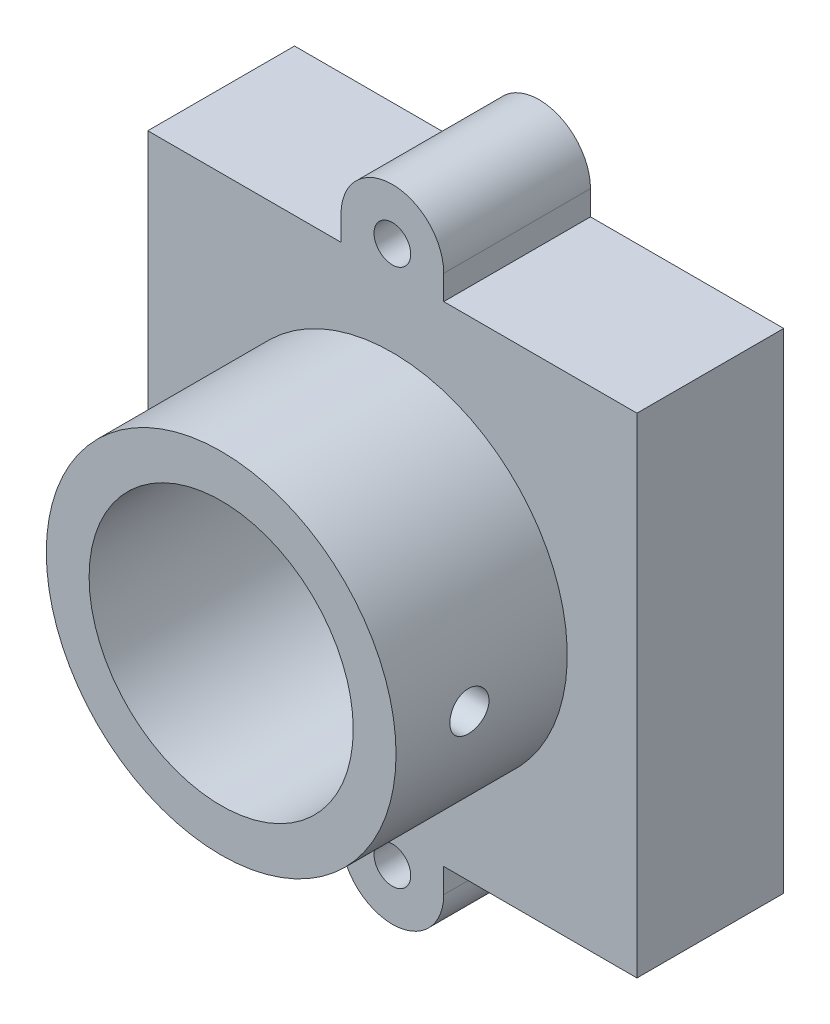
SolidWorks part; units mm, degrees
ref_plane "Ebene vorne" through (0, 0, 0) normal (0, 0, 1) x (1, 0, 0)
ref_plane "Ebene oben" through (0, 0, 0) normal (0, 1, 0) x (1, 0, 0)
ref_plane "Ebene rechts" through (0, 0, 0) normal (1, 0, 0) x (0, 0, -1)
ref_plane "Ebene1" through (0, 0, 0) normal (0, 0, -1) x (-1, 0, 0)
sketch "Skizze1" plane through (0, 0, 0) normal (0, 0, -1) x (-1, 0, 0)
  line L0 (2.1, -11) -> (2.1, 11)
  line L1 (-2.1, 11) -> (-2.1, -11)
  arc A0 (-2.1, -11) -> (2.1, -11) centre (0, -11) ccw
  arc A1 (2.1, 11) -> (-2.1, 11) centre (0, 11) ccw
extrude "Aufsatz-Linear austragen1" add sketch "Skizze1" against normal blind 6
sketch "Skizze2" plane through (-2.1, 0, 0) normal (-1, 0, 0) x (0, 0, 1)
  line L0 (6, -10) -> (0, -10)
  line L1 (0, -10) -> (0, 10)
  line L2 (0, 10) -> (6, 10)
  line L3 (6, 10) -> (6, -10)
extrude "Aufsatz-Linear austragen2" add sketch "Skizze2" along normal blind 7.9
sketch "Skizze3" plane through (2.1, 0, 0) normal (1, 0, 0) x (0, 0, -1)
  line L0 (-6, 10) -> (0, 10)
  line L1 (0, 10) -> (0, -10)
  line L2 (0, -10) -> (-6, -10)
  line L3 (-6, -10) -> (-6, 10)
extrude "Aufsatz-Linear austragen3" add sketch "Skizze3" along normal blind 7.9
sketch "Skizze4" plane through (0, 0, 6) normal (0, 0, 1) x (1, 0, 0)
  circle A0 centre (0, 0) radius 7.15
extrude "Aufsatz-Linear austragen4" add sketch "Skizze4" along normal blind 7
sketch "Skizze5" plane through (0, 0, 0) normal (0, 0, -1) x (-1, 0, 0)
  line L0 (-9.5, 9.5) -> (-9.5, -9.5)
  line L1 (-9.5, -9.5) -> (9.5, -9.5)
  line L2 (9.5, -9.5) -> (9.5, 9.5)
  line L3 (9.5, 9.5) -> (-9.5, 9.5)
extrude "Schnitt-Linear austragen1" cut sketch "Skizze5" against normal blind 1.3
sketch "Skizze6" plane through (0, 0, 1.3) normal (0, 0, -1) x (-1, 0, 0)
  line L0 (9, -9) -> (9, 9)
  line L1 (9, 9) -> (-9, 9)
  line L2 (-9, 9) -> (-9, -9)
  line L3 (-9, -9) -> (9, -9)
extrude "Schnitt-Linear austragen2" cut sketch "Skizze6" against normal blind 3.7
hole_wizard "Ø1.5 (1.5) Durchmesser Bohrung1" positions "Skizze8" profile "Skizze7" hole size "Ø1.5" standard "Ansi Metrisch"
sketch "Skizze8" plane through (0, 0, 0) normal (0, 0, -1) x (-1, 0, 0)
  point P0 (0, -11)
  point P1 (0, 11)
sketch "Skizze7" plane through (0, -11, 0) normal (1, 0, 0) x (0, 1, 0)
  line L0 (0, 0) -> (0, 13)
  line L1 (0, 13) -> (0.75, 13)
  line L2 (0.75, 13) -> (0.75, 0)
  line L5 (0.75, 0) -> (0, 0)
  line L11 (0, -6.35) -> (0, 107.95) construction
  dimension "Bohrerdurchmesser" = 1.5
  dimension "Bohrungstiefe" = 13
hole_wizard "Ø10.8 (10.8) Durchmesser Bohrung1" positions "Skizze10" profile "Skizze9" hole size "Ø10.8" standard "Ansi Metrisch"
sketch "Skizze10" plane through (0, 0, 13) normal (0, 0, 1) x (1, 0, 0)
  point P0 (0, 0)
sketch "Skizze9" plane through (0, 0, 13) normal (1, 0, 0) x (0, -1, 0)
  line L0 (0, 0) -> (0, 13)
  line L1 (0, 13) -> (5.4, 13)
  line L2 (5.4, 13) -> (5.4, 0)
  line L5 (5.4, 0) -> (0, 0)
  line L11 (0, -6.35) -> (0, 107.95) construction
  dimension "Bohrerdurchmesser" = 10.8
  dimension "Bohrungstiefe" = 13
hole_wizard "Ø1.6 (1.6) Durchmesser Bohrung1" positions "3D-Skizze1" profile "Skizze11" hole size "Ø1.6" standard "Ansi Metrisch"
sketch3d "3D-Skizze1"
  point P0 (7.15, 0, 10)
sketch "Skizze11" plane through (7.15, 0, 10) normal (0, 1, 0) x (0, 0, -1)
  line L0 (0, 0) -> (0, 1.75)
  line L1 (0, 1.75) -> (0.8, 1.75)
  line L2 (0.8, 1.75) -> (0.8, 0)
  line L5 (0.8, 0) -> (0, 0)
  line L11 (0, -6.35) -> (0, 107.95) construction
  dimension "Bohrerdurchmesser" = 1.6
  dimension "Bohrungstiefe" = 1.75
chamfer "Fase1" distance 2 angle 45 4 edges at (9, -9, 3.15) (-9, 9, 3.15) (9, 9, 3.15) (-9, -9, 3.15)
chamfer "Fase2" distance 2.2929 angle 45 4 edges at (-9.5, 9.5, 0.65) (9.5, -9.5, 0.65) (9.5, 9.5, 0.65) (-9.5, -9.5, 0.65)
